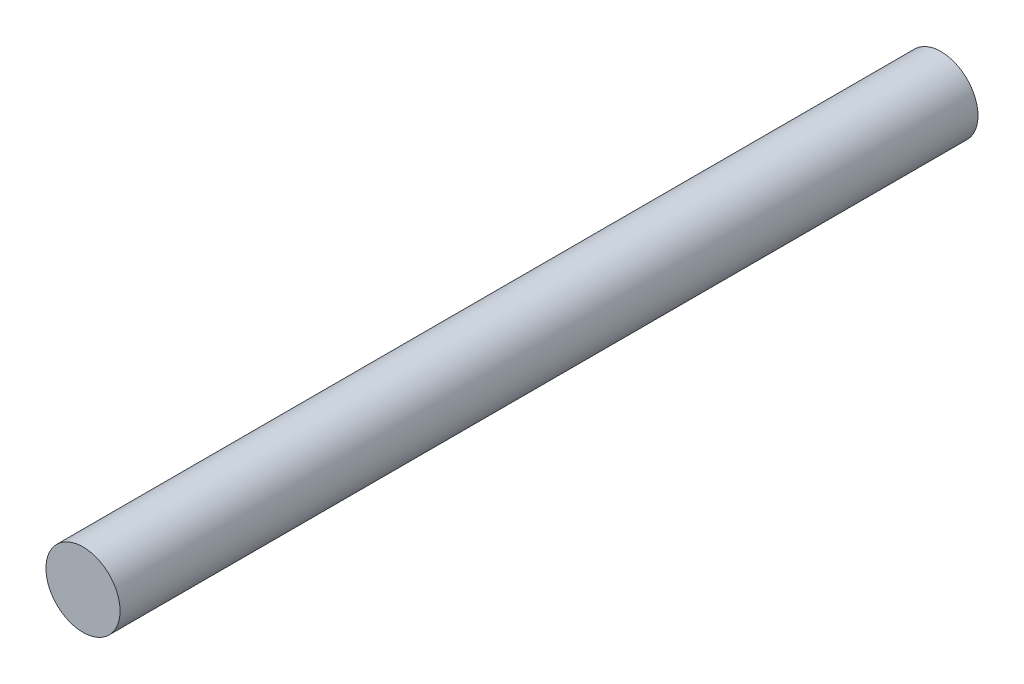
SolidWorks part; units mm, degrees
material "Hierro dúctil"
ref_plane "Alzado" through (0, 0, 0) normal (0, 0, 1) x (1, 0, 0)
ref_plane "Planta" through (0, 0, 0) normal (0, 1, 0) x (1, 0, 0)
ref_plane "Vista lateral" through (0, 0, 0) normal (1, 0, 0) x (0, 0, -1)
sketch "Croquis1" plane through (0, 0, 0) normal (0, 0, 1) x (1, 0, 0)
  circle A0 centre (0, 0) radius 4.75
  dimension "D1" = 9.5
extrude "Saliente-Extruir1" add sketch "Croquis1" along normal blind 110
